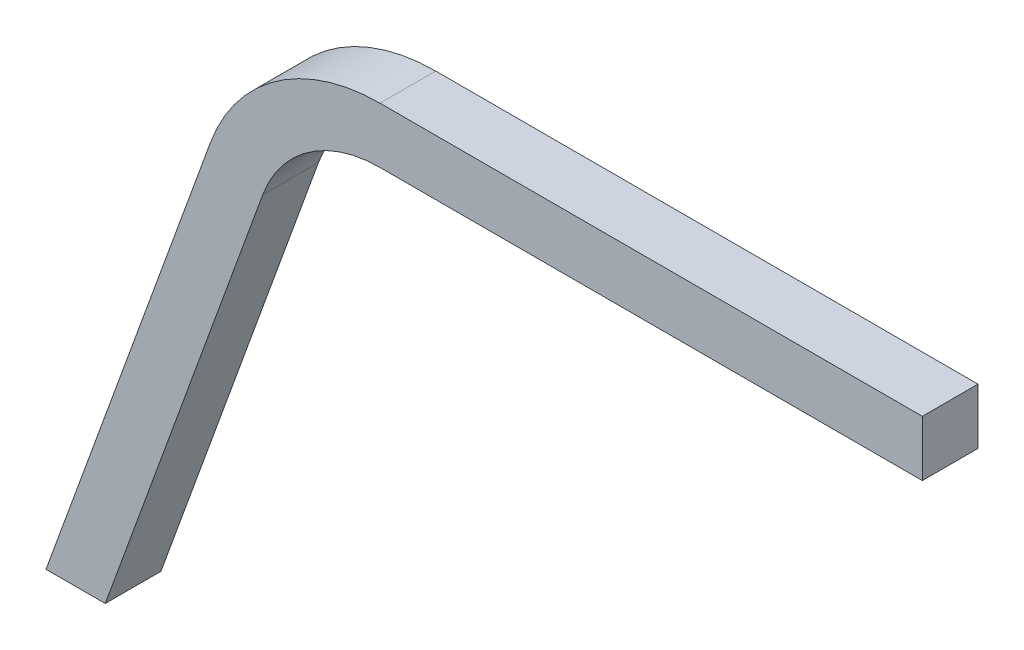
SolidWorks part; units mm, degrees
ref_plane "Front Plane" through (0, 0, 0) normal (0, 0, 1) x (1, 0, 0)
ref_plane "Top Plane" through (0, 0, 0) normal (0, 1, 0) x (1, 0, 0)
ref_plane "Right Plane" through (0, 0, 0) normal (1, 0, 0) x (0, 0, -1)
sketch "Sketch1" plane through (0, 0, 0) normal (0, 0, 1) x (1, 0, 0)
  line L0 (99.949, 65.0875) -> (99.949, 58.7375)
  line L1 (99.949, 0) -> (6.7575, 0) construction
  line L2 (99.949, 65.0875) -> (38.1, 65.0875)
  line L3 (0, 0) -> (0, 94.7944) construction
  line L4 (0, 0) -> (18.7614, 51.5464)
  line L5 (99.949, 58.7375) -> (38.1, 58.7375)
  line L6 (6.7575, 0) -> (24.7284, 49.3746)
  line L7 (5.967, -2.1718) -> (24.7284, 49.3746) construction
  line L8 (6.7575, 0) -> (0, 0)
  line L9 (99.949, 58.7375) -> (99.949, 0) construction
  arc A0 (18.7614, 51.5464) -> (38.1, 65.0875) centre (38.1, 44.5078) cw
  arc A1 (24.7284, 49.3746) -> (38.1, 58.7375) centre (38.1, 44.5078) cw
  point P14 (0, 0)
  dimension "D1" = 65.0875
  dimension "D2" = 99.949
  dimension "D3" = 61.849
  dimension "D4" = 70
  dimension "D5" = 6.35
extrude "Extrude1" add sketch "Sketch1" along normal blind 6.35
